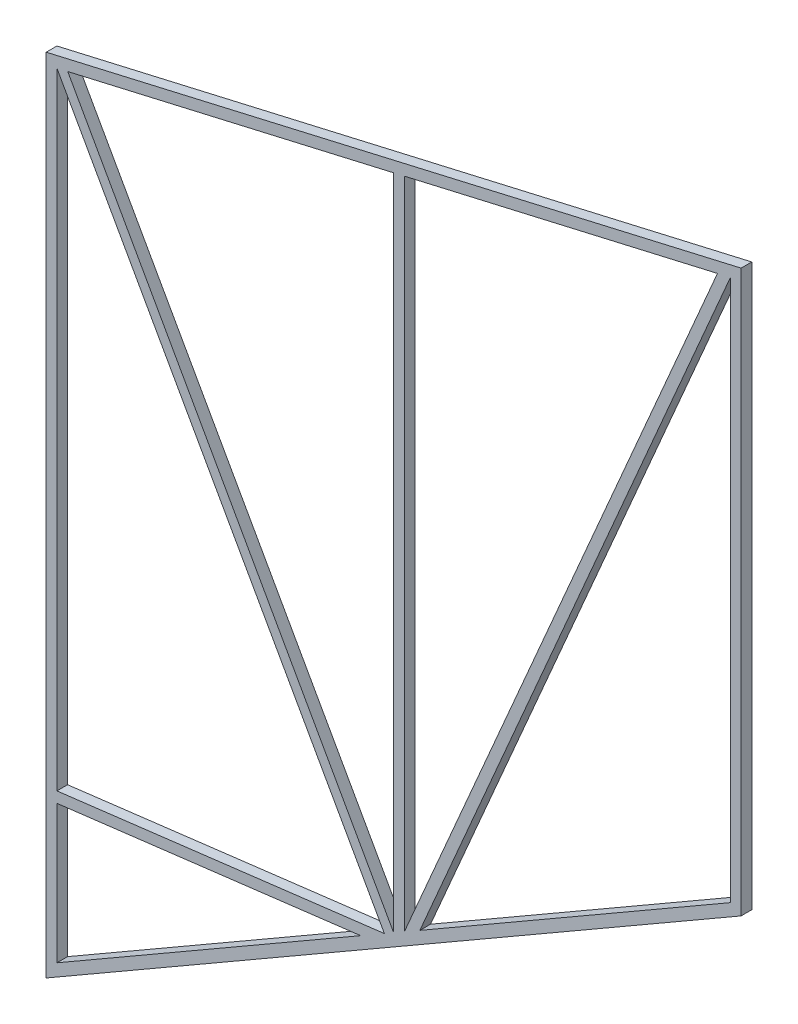
SolidWorks part; units mm, degrees
material "ﾊﾞﾙｻ"
ref_plane "正面" through (0, 0, 0) normal (0, 0, 1) x (1, 0, 0)
ref_plane "平面" through (0, 0, 0) normal (0, 1, 0) x (1, 0, 0)
ref_plane "右側面" through (0, 0, 0) normal (1, 0, 0) x (0, 0, -1)
sketch "ｽｹｯﾁ1" plane through (0, 0, 0) normal (0, 0, 1) x (1, 0, 0)
  line L0 (0, 0) -> (0, 150)
  line L1 (0, 150) -> (130, 180.0129)
  line L2 (130, 180.0129) -> (130, 75.0555)
  line L3 (130, 75.0555) -> (0, 0)
  line L4 (0, 0) -> (165.5945, 0) construction
  line L5 (2, 148.4091) -> (128, 177.4985)
  line L6 (128, 177.4985) -> (128, 76.2102)
  line L7 (128, 76.2102) -> (2, 3.4641)
  line L8 (2, 3.4641) -> (2, 148.4091)
  line L9 (65, 162.9538) -> (65, 39.8372)
  line L10 (67, 163.4156) -> (67, 40.9919)
  line L11 (2, 148.4091) -> (63.2678, 38.8371)
  line L12 (4.0294, 148.8777) -> (65, 39.8372)
  line L13 (67, 40.9919) -> (125.5816, 176.9402)
  line L14 (128, 177.4985) -> (69.899, 42.6656)
  line L15 (2, 31.3143) -> (63.2678, 38.8371)
  line L16 (2, 29.2993) -> (58.8349, 36.2778)
  point P21 (30.4175, 32.7885)
  dimension "D1" = 150
  dimension "D2" = 130
  dimension "D3" = 30
  dimension "D4" = 13
  dimension "D6" = 2
  dimension "D7" = 2
  dimension "D8" = 65
  dimension "D9" = 2
  dimension "D10" = 2
  dimension "D11" = 83
  dimension "D5" = 2
extrude "ﾎﾞｽ - 押し出し1" add sketch "ｽｹｯﾁ1" along normal blind 2 contours L3 L2 L1 L0 L7 L8 L5 L6 | L10 L5 L9 L7 | L12 L5 L11 L7 | L14 L5 L13 L7 | L8 L16 L7 L15
